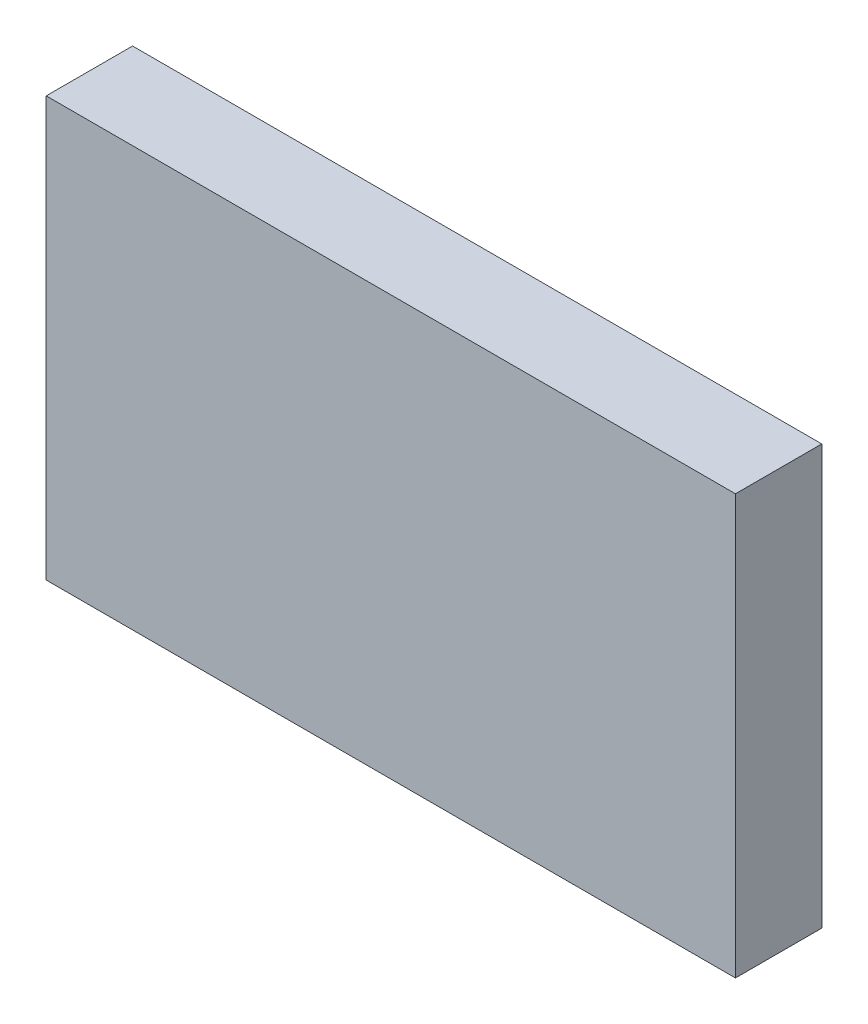
SolidWorks part; units mm, degrees
ref_plane "Front Plane" through (0, 0, 0) normal (0, 0, 1) x (1, 0, 0)
ref_plane "Top Plane" through (0, 0, 0) normal (0, 1, 0) x (1, 0, 0)
ref_plane "Right Plane" through (0, 0, 0) normal (1, 0, 0) x (0, 0, -1)
sketch "Sketch1" plane through (0, 0, 0) normal (0, 1, 0) x (1, 0, 0)
  line L1 (13.97, -1.75) -> (-13.97, -1.75)
  line L2 (13.97, -1.75) -> (13.97, 1.75)
  line L3 (13.97, 1.75) -> (-13.97, 1.75)
  line L4 (-13.97, -1.75) -> (-13.97, 1.75)
  line L5 (13.97, -1.75) -> (-13.97, 1.75) construction
  line L6 (13.97, 1.75) -> (-13.97, -1.75) construction
  point P0 (0, 0)
  dimension "D1" = 27.94
  dimension "D2" = 3.5
extrude "Boss-Extrude1" add sketch "Sketch1" along normal blind 17
